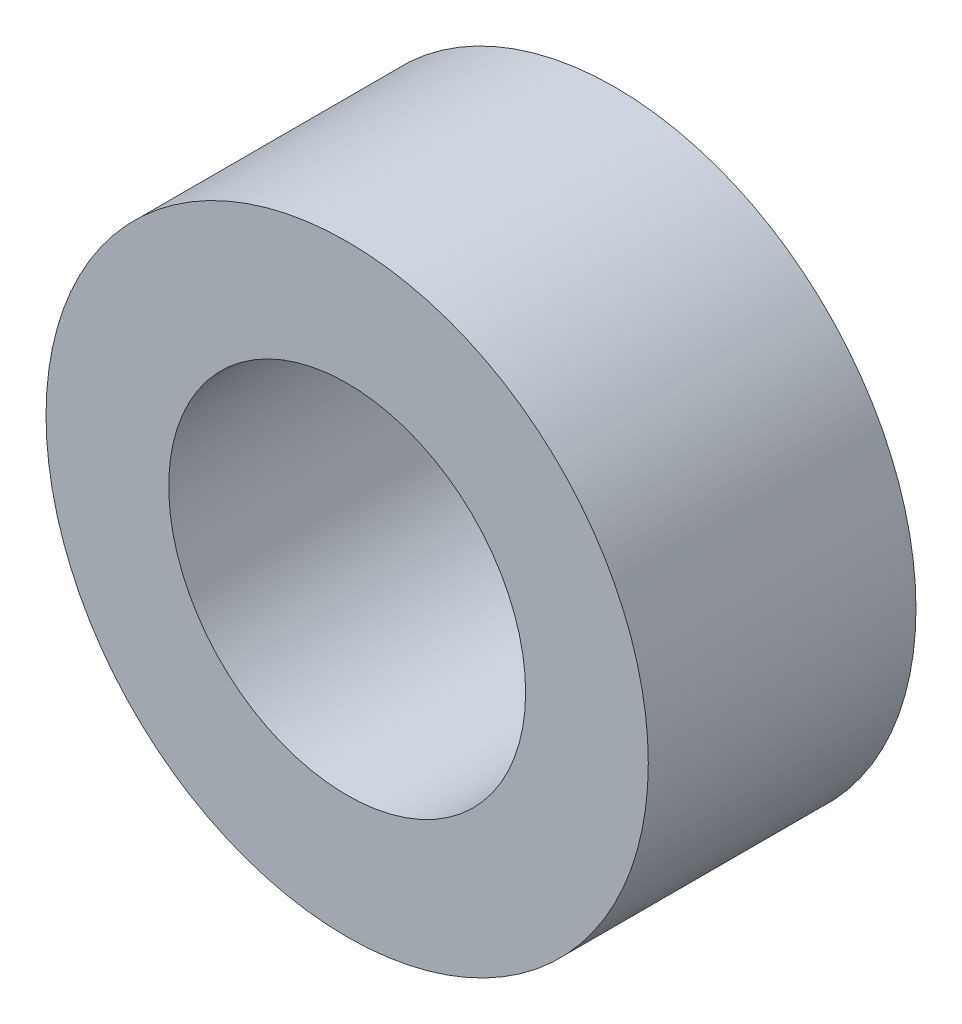
SolidWorks part; units mm, degrees
ref_plane "Alzado" through (0, 0, 0) normal (0, 0, 1) x (1, 0, 0)
ref_plane "Planta" through (0, 0, 0) normal (0, 1, 0) x (1, 0, 0)
ref_plane "Vista lateral" through (0, 0, 0) normal (1, 0, 0) x (0, 0, -1)
sketch "Croquis1" plane through (0, 0, 0) normal (0, 0, 1) x (1, 0, 0)
  circle A0 centre (0, 0) radius 94.5
  dimension "D1" = 189
extrude "Saliente-Extruir1" add sketch "Croquis1" along normal blind 84
sketch "Croquis2" plane through (0, 0, 84) normal (0, 0, 1) x (1, 0, 0)
  circle A0 centre (0, 0) radius 56
  dimension "D1" = 112
extrude "Cortar-Extruir1" cut sketch "Croquis2" against normal blind 84
